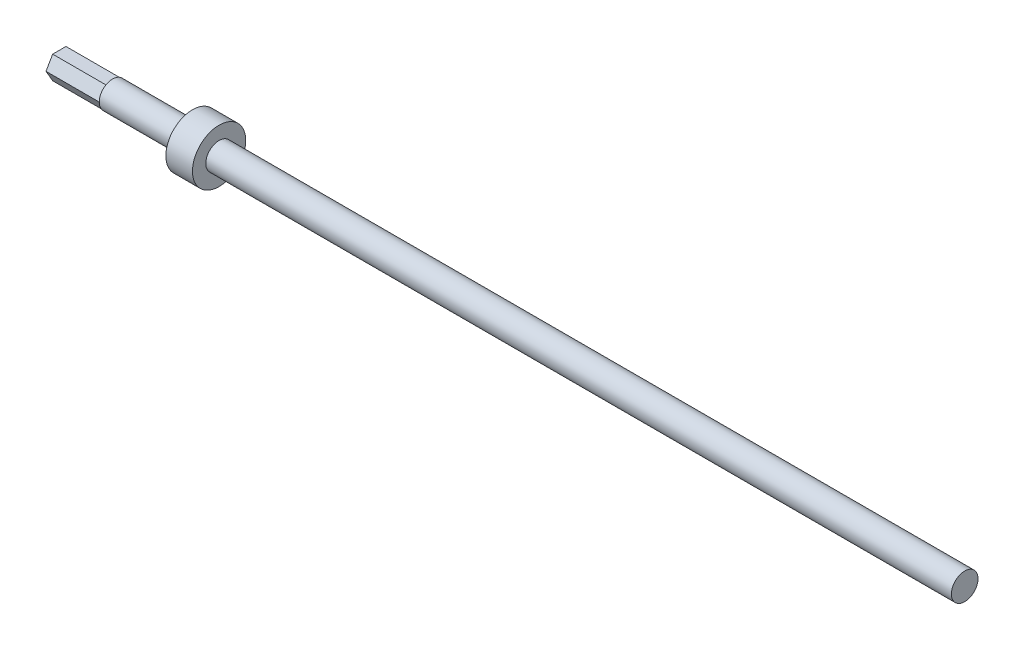
SolidWorks part; units mm, degrees
ref_plane "Front Plane" through (0, 0, 0) normal (0, 0, 1) x (1, 0, 0)
ref_plane "Top Plane" through (0, 0, 0) normal (0, 1, 0) x (1, 0, 0)
ref_plane "Right Plane" through (0, 0, 0) normal (1, 0, 0) x (0, 0, -1)
sketch "Sketch1" plane through (0, 0, 0) normal (0, 0, 1) x (1, 0, 0)
  line L0 (-42.0558, 0) -> (410.9878, 0) construction
  line L1 (369.2196, 6.35) -> (369.2196, 0)
  line L2 (-37.1804, 0) -> (369.2196, 0)
  line L3 (-37.1804, 0) -> (-37.1804, 6.35)
  line L4 (-37.1804, 6.35) -> (0.9196, 6.35)
  line L5 (0.9196, 6.35) -> (0.9196, 12.7)
  line L6 (0.9196, 12.7) -> (13.6196, 12.7)
  line L7 (13.6196, 12.7) -> (13.6196, 6.35)
  line L8 (13.6196, 6.35) -> (369.2196, 6.35)
  dimension "D1" = 6.35
  dimension "D2" = 38.1
  dimension "D3" = 6.35
  dimension "D4" = 12.7
  dimension "D5" = 406.4
revolve "Revolve1" add sketch "Sketch1" angle 360 about L0
sketch "Sketch2" plane through (-37.1804, 0, 0) normal (-1, 0, 0) x (0, 0, 1)
  line L1 (3.175, -5.4993) -> (6.35, 0)
  line L2 (6.35, 0) -> (3.175, 5.4993)
  line L3 (3.175, 5.4993) -> (-3.175, 5.4993)
  line L4 (-3.175, 5.4993) -> (-6.35, 0)
  line L5 (-6.35, 0) -> (-3.175, -5.4993)
  line L6 (-3.175, -5.4993) -> (3.175, -5.4993)
  circle A0 centre (0, 0) radius 5.4993 construction
  circle A1 centre (0, 0) radius 6.35 construction
extrude "Boss-Extrude1" add sketch "Sketch2" along normal blind 25.4
